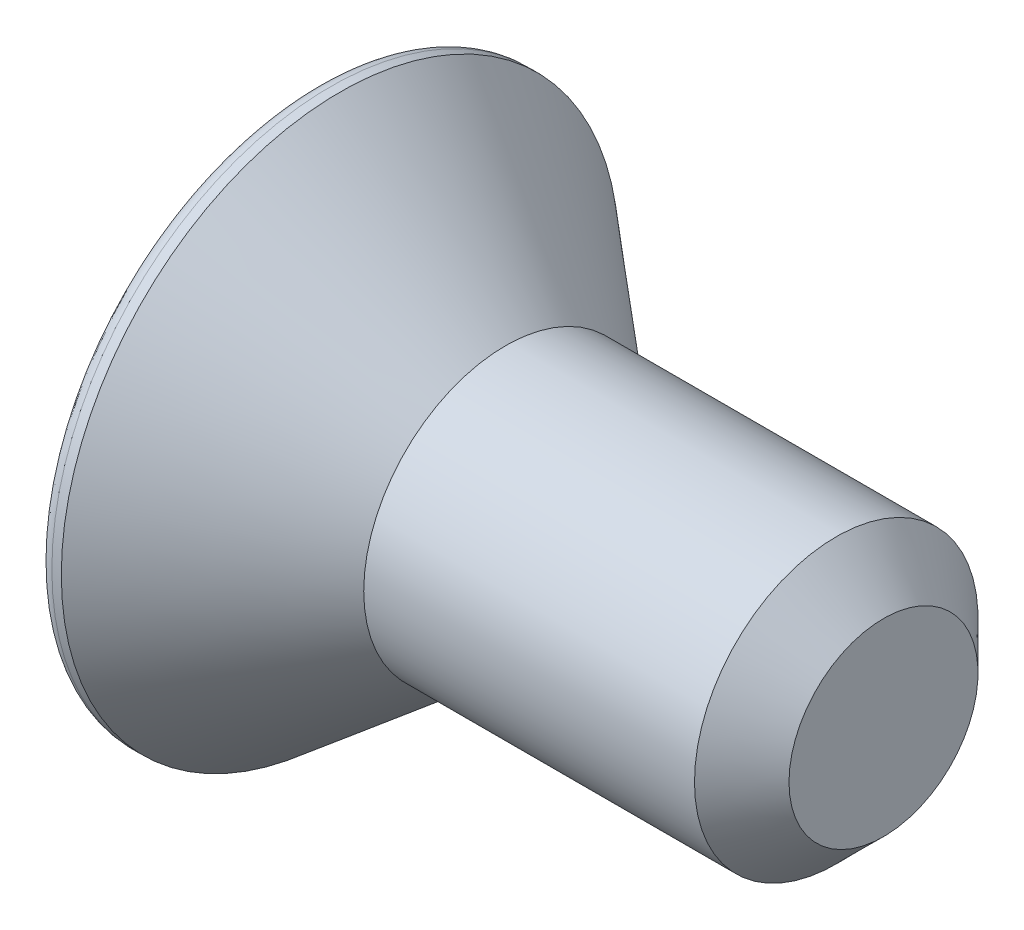
SolidWorks part; units mm, degrees
ref_plane "Спереди" through (0, 0, 0) normal (0, 0, 1) x (1, 0, 0)
ref_plane "Сверху" through (0, 0, 0) normal (0, 1, 0) x (1, 0, 0)
ref_plane "Справа" through (0, 0, 0) normal (1, 0, 0) x (0, 0, -1)
sketch "Эскиз1" plane through (0, 0, 0) normal (0, 0, 1) x (1, 0, 0)
  line L0 (0, 0) -> (0, 5.9)
  line L1 (0.5, 5.9) -> (4, 3)
  line L3 (4, 3) -> (12, 3)
  line L4 (12, 3) -> (12, 0)
  line L6 (0, 0) -> (12, 0)
  line L8 (0, 5.9) -> (0.5, 5.9)
  line L9 (0, 0) -> (-3.6011, 0) construction
  dimension "D4" = 0.5
  dimension "D1" = 4
  dimension "D2" = 11.8
  dimension "D3" = 6
  dimension "D5" = 12
revolve "Повернуть1" add sketch "Эскиз1" angle 360 about L6
cosmetic thread "Условное изображение резьбы1" parameters "D2"=4.891
sketch "Эскиз2" plane through (0, 0, 0) normal (-1, 0, 0) x (0, 0, 1)
  line L1 (1.1547, 2) -> (-1.1547, 2)
  line L2 (-1.1547, 2) -> (-2.3094, 0)
  line L3 (-2.3094, 0) -> (-1.1547, -2)
  line L4 (-1.1547, -2) -> (1.1547, -2)
  line L5 (1.1547, -2) -> (2.3094, 0)
  line L6 (2.3094, 0) -> (1.1547, 2)
  circle A0 centre (0, 0) radius 2 construction
  dimension "D1" = 4
extrude "Вырез-Вытянуть1" cut sketch "Эскиз2" against normal blind 3
fillet "Скругление1" radius 0.3 1 edges at (0, 0, 5.9)
chamfer "Фаска1" distance 1 angle 45 1 edges at (12, 0, 3)
